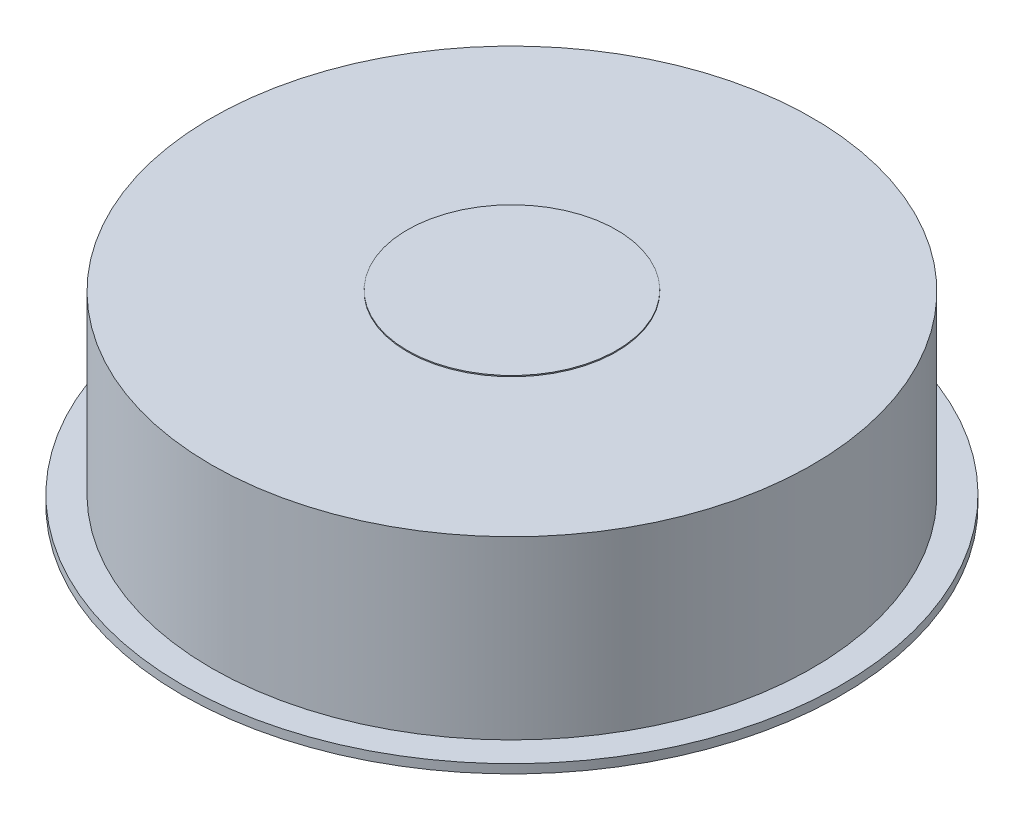
SolidWorks part; units mm, degrees
material "Polyethylene Cross-Linked"
ref_plane "Front Plane" through (0, 0, 0) normal (0, 0, 1) x (1, 0, 0)
ref_plane "Top Plane" through (0, 0, 0) normal (0, 1, 0) x (1, 0, 0)
ref_plane "Right Plane" through (0, 0, 0) normal (1, 0, 0) x (0, 0, -1)
sketch "Sketch1" plane through (0, 0, 0) normal (0, 1, 0) x (1, 0, 0)
  circle A0 centre (0, 0) radius 61.3
extrude "Boss-Extrude1" add sketch "Sketch1" along normal blind 1.65
sketch "Sketch2" plane through (0, 1.65, 0) normal (0, 1, 0) x (1, 0, 0)
  circle A0 centre (0, 0) radius 55.89
  dimension "D1" = 111.78
extrude "Boss-Extrude2" add sketch "Sketch2" along normal blind 32.735
sketch "Sketch3" plane through (0, 0, 0) normal (0, -1, 0) x (1, 0, 0)
  circle A0 centre (0, 0) radius 50.86
  dimension "D1" = 101.72
extrude "Cut-Extrude1" cut sketch "Sketch3" against normal blind 14.35
sketch "Sketch5" plane through (0, 34.385, 0) normal (0, 1, 0) x (1, 0, 0)
  circle A0 centre (0, 0) radius 19.45
extrude "Boss-Extrude3" add sketch "Sketch5" along normal blind 0.2
scale "Scale2" scale about centroid uniform scaling yes scale factor 0.5
